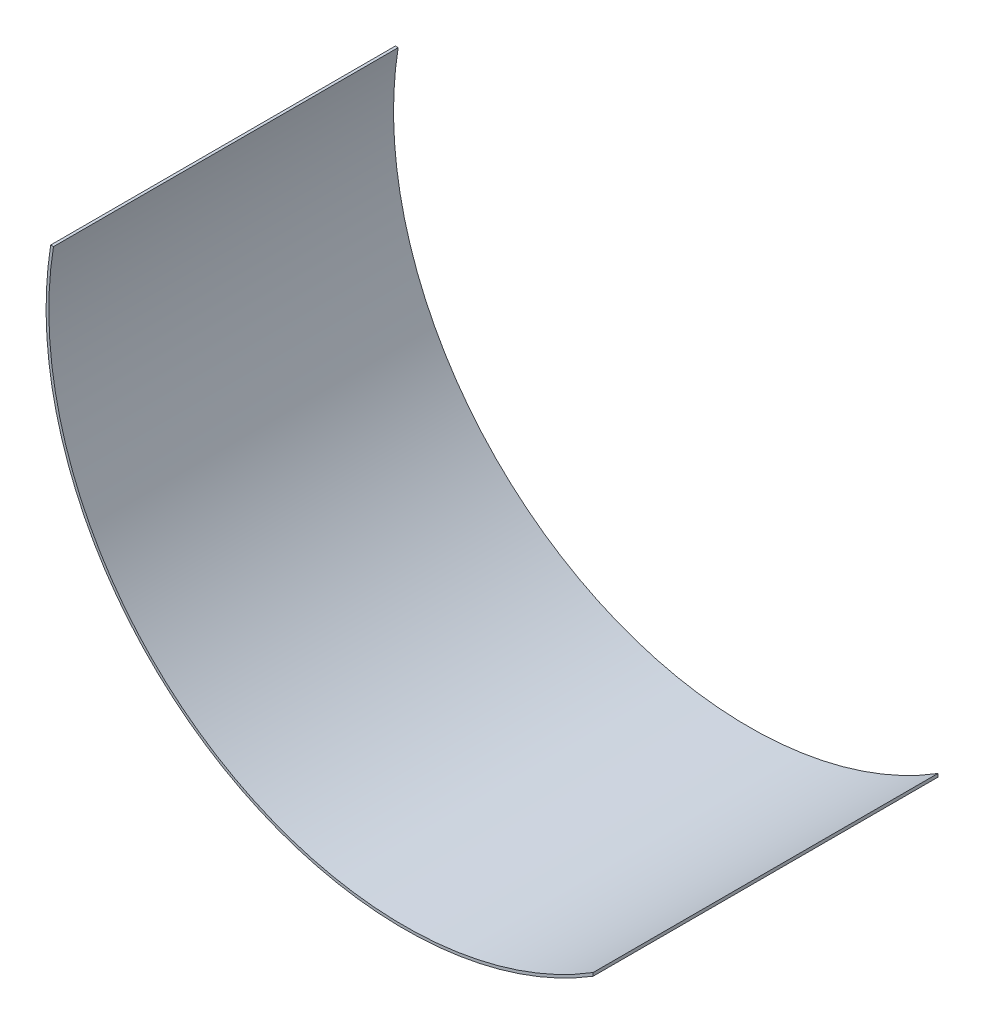
SolidWorks part; units mm, degrees
ref_plane "Front Plane" through (0, 0, 0) normal (0, 0, 1) x (1, 0, 0)
ref_plane "Top Plane" through (0, 0, 0) normal (0, 1, 0) x (1, 0, 0)
ref_plane "Right Plane" through (0, 0, 0) normal (1, 0, 0) x (0, 0, -1)
sketch "Sketch1" plane through (0, 0, 0) normal (0, 0, 1) x (1, 0, 0)
  circle A2 centre (-31.5327, 19.9145) radius 165.0623
extrude "Boss-Extrude1" add sketch "Sketch1" along normal blind 158.75 contours A2
shell "Shell1" thickness 1.27
sketch "Sketch2" plane through (0, 0, 158.75) normal (0, 0, 1) x (1, 0, 0)
  line L1 (55.3996, -154.3901) -> (218.5443, -154.3901)
  line L2 (55.3996, -154.3901) -> (55.3996, 240.223)
  line L3 (55.3996, 240.223) -> (218.5443, 240.223)
  line L4 (218.5443, -154.3901) -> (218.5443, 240.223)
extrude "Cut-Extrude2" cut sketch "Sketch2" against normal blind 158.75 contours L2 L1 L4 L3
sketch "Sketch3" plane through (0, 0, 158.75) normal (0, 0, 1) x (1, 0, 0)
  line L1 (-216.3091, 207.0249) -> (146.3133, 207.0249)
  line L2 (-216.3091, 207.0249) -> (-216.3091, 46.3148)
  line L3 (-216.3091, 46.3148) -> (146.3133, 46.3148)
  line L4 (146.3133, 207.0249) -> (146.3133, 46.3148)
extrude "Cut-Extrude3" cut sketch "Sketch3" against normal blind 158.75
